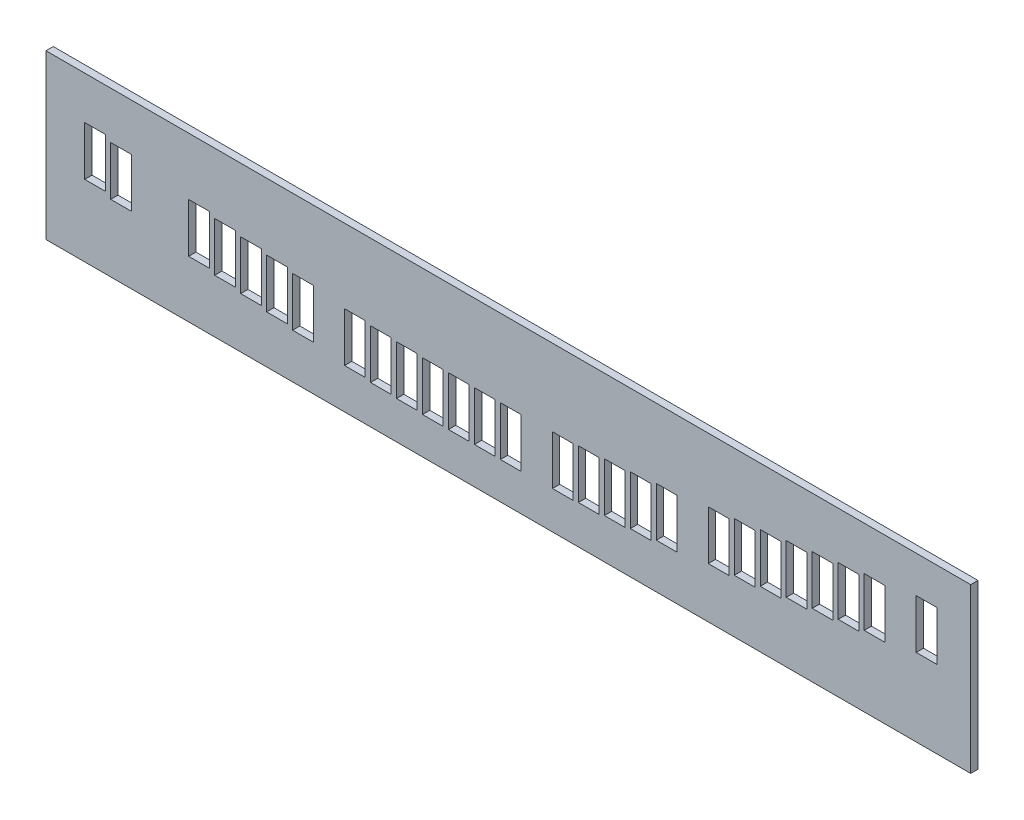
SolidWorks part; units mm, degrees
ref_plane "Front Plane" through (0, 0, 0) normal (0, 0, 1) x (1, 0, 0)
ref_plane "Top Plane" through (0, 0, 0) normal (0, 1, 0) x (1, 0, 0)
ref_plane "Right Plane" through (0, 0, 0) normal (1, 0, 0) x (0, 0, -1)
sketch "Sketch1" plane through (0, 0, 0) normal (0, 0, 1) x (1, 0, 0)
  line L0 (-0.0001, 1146.0049) -> (1685.9999, 1146.0049)
  line L1 (19.0499, 859.7049) -> (1666.8999, 859.7049)
  line L2 (-0.0001, 1146.0049) -> (-0.0001, 0)
  line L3 (19.0499, 1146.0049) -> (19.0499, 0)
  line L4 (104.9999, 1018.5049) -> (104.9999, 1092.5049)
  line L5 (104.9999, 1092.5049) -> (74.9999, 1092.5049)
  line L6 (74.9999, 1092.5049) -> (74.9999, 1018.5049)
  line L7 (74.9999, 1018.5049) -> (104.9999, 1018.5049)
  line L8 (1666.9499, 1146.0049) -> (1666.9499, 0)
  line L9 (1647.8999, 1146.0049) -> (1647.8999, 859.7049) construction
  line L10 (1685.9999, 1146.0049) -> (1685.9999, 0)
  line L11 (38.0999, 1146.0049) -> (38.0999, 859.7049) construction
  line L12 (143.9999, 992.5049) -> (173.9999, 992.5049)
  line L13 (173.9999, 992.5049) -> (173.9999, 918.5049)
  line L14 (173.9999, 918.5049) -> (143.9999, 918.5049)
  line L15 (143.9999, 918.5049) -> (143.9999, 992.5049)
  line L16 (189.9999, 992.5049) -> (219.9999, 992.5049)
  line L17 (219.9999, 992.5049) -> (219.9999, 918.5049)
  line L18 (219.9999, 918.5049) -> (189.9999, 918.5049)
  line L19 (189.9999, 918.5049) -> (189.9999, 992.5049)
  line L20 (235.9999, 992.5049) -> (265.9999, 992.5049)
  line L21 (265.9999, 992.5049) -> (265.9999, 918.5049)
  line L22 (265.9999, 918.5049) -> (235.9999, 918.5049)
  line L23 (235.9999, 918.5049) -> (235.9999, 992.5049)
  line L24 (196.9999, 1018.5049) -> (196.9999, 1092.5049)
  line L25 (196.9999, 1092.5049) -> (166.9999, 1092.5049)
  line L26 (166.9999, 1092.5049) -> (166.9999, 1018.5049)
  line L27 (166.9999, 1018.5049) -> (196.9999, 1018.5049)
  line L28 (242.9999, 1018.5049) -> (242.9999, 1092.5049)
  line L29 (242.9999, 1092.5049) -> (212.9999, 1092.5049)
  line L30 (212.9999, 1092.5049) -> (212.9999, 1018.5049)
  line L31 (212.9999, 1018.5049) -> (242.9999, 1018.5049)
  line L32 (281.9999, 992.5049) -> (311.9999, 992.5049)
  line L33 (311.9999, 992.5049) -> (311.9999, 918.5049)
  line L34 (311.9999, 918.5049) -> (281.9999, 918.5049)
  line L35 (281.9999, 918.5049) -> (281.9999, 992.5049)
  line L36 (327.9999, 992.5049) -> (357.9999, 992.5049)
  line L37 (357.9999, 992.5049) -> (357.9999, 918.5049)
  line L38 (357.9999, 918.5049) -> (327.9999, 918.5049)
  line L39 (327.9999, 918.5049) -> (327.9999, 992.5049)
  line L40 (373.9999, 992.5049) -> (403.9999, 992.5049)
  line L41 (403.9999, 992.5049) -> (403.9999, 918.5049)
  line L42 (403.9999, 918.5049) -> (373.9999, 918.5049)
  line L43 (373.9999, 918.5049) -> (373.9999, 992.5049)
  line L44 (419.9999, 992.5049) -> (449.9999, 992.5049)
  line L45 (449.9999, 992.5049) -> (449.9999, 918.5049)
  line L46 (449.9999, 918.5049) -> (419.9999, 918.5049)
  line L47 (419.9999, 918.5049) -> (419.9999, 992.5049)
  line L48 (334.9999, 1018.5049) -> (334.9999, 1092.5049)
  line L49 (334.9999, 1092.5049) -> (304.9999, 1092.5049)
  line L50 (304.9999, 1092.5049) -> (304.9999, 1018.5049)
  line L51 (304.9999, 1018.5049) -> (334.9999, 1018.5049)
  line L52 (380.9999, 1018.5049) -> (380.9999, 1092.5049)
  line L53 (380.9999, 1092.5049) -> (350.9999, 1092.5049)
  line L54 (350.9999, 1092.5049) -> (350.9999, 1018.5049)
  line L55 (350.9999, 1018.5049) -> (380.9999, 1018.5049)
  line L56 (426.9999, 1018.5049) -> (426.9999, 1092.5049)
  line L57 (426.9999, 1092.5049) -> (396.9999, 1092.5049)
  line L58 (396.9999, 1092.5049) -> (396.9999, 1018.5049)
  line L59 (396.9999, 1018.5049) -> (426.9999, 1018.5049)
  line L60 (465.9999, 992.5049) -> (495.9999, 992.5049)
  line L61 (495.9999, 992.5049) -> (495.9999, 918.5049)
  line L62 (495.9999, 918.5049) -> (465.9999, 918.5049)
  line L63 (465.9999, 918.5049) -> (465.9999, 992.5049)
  line L64 (511.9999, 992.5049) -> (541.9999, 992.5049)
  line L65 (541.9999, 992.5049) -> (541.9999, 918.5049)
  line L66 (541.9999, 918.5049) -> (511.9999, 918.5049)
  line L67 (511.9999, 918.5049) -> (511.9999, 992.5049)
  line L68 (557.9999, 992.5049) -> (587.9999, 992.5049)
  line L69 (587.9999, 992.5049) -> (587.9999, 918.5049)
  line L70 (587.9999, 918.5049) -> (557.9999, 918.5049)
  line L71 (557.9999, 918.5049) -> (557.9999, 992.5049)
  line L72 (518.9999, 1018.5049) -> (518.9999, 1092.5049)
  line L73 (518.9999, 1092.5049) -> (488.9999, 1092.5049)
  line L74 (488.9999, 1092.5049) -> (488.9999, 1018.5049)
  line L75 (488.9999, 1018.5049) -> (518.9999, 1018.5049)
  line L76 (564.9999, 1018.5049) -> (564.9999, 1092.5049)
  line L77 (564.9999, 1092.5049) -> (534.9999, 1092.5049)
  line L78 (534.9999, 1092.5049) -> (534.9999, 1018.5049)
  line L79 (534.9999, 1018.5049) -> (564.9999, 1018.5049)
  line L80 (603.9999, 992.5049) -> (633.9999, 992.5049)
  line L81 (633.9999, 992.5049) -> (633.9999, 918.5049)
  line L82 (633.9999, 918.5049) -> (603.9999, 918.5049)
  line L83 (603.9999, 918.5049) -> (603.9999, 992.5049)
  line L84 (649.9999, 992.5049) -> (679.9999, 992.5049)
  line L85 (679.9999, 992.5049) -> (679.9999, 918.5049)
  line L86 (679.9999, 918.5049) -> (649.9999, 918.5049)
  line L87 (649.9999, 918.5049) -> (649.9999, 992.5049)
  line L88 (695.9999, 992.5049) -> (725.9999, 992.5049)
  line L89 (725.9999, 992.5049) -> (725.9999, 918.5049)
  line L90 (725.9999, 918.5049) -> (695.9999, 918.5049)
  line L91 (695.9999, 918.5049) -> (695.9999, 992.5049)
  line L92 (741.9999, 992.5049) -> (771.9999, 992.5049)
  line L93 (771.9999, 992.5049) -> (771.9999, 918.5049)
  line L94 (771.9999, 918.5049) -> (741.9999, 918.5049)
  line L95 (741.9999, 918.5049) -> (741.9999, 992.5049)
  line L96 (656.9999, 1018.5049) -> (656.9999, 1092.5049)
  line L97 (656.9999, 1092.5049) -> (626.9999, 1092.5049)
  line L98 (626.9999, 1092.5049) -> (626.9999, 1018.5049)
  line L99 (626.9999, 1018.5049) -> (656.9999, 1018.5049)
  line L100 (702.9999, 1018.5049) -> (702.9999, 1092.5049)
  line L101 (702.9999, 1092.5049) -> (672.9999, 1092.5049)
  line L102 (672.9999, 1092.5049) -> (672.9999, 1018.5049)
  line L103 (672.9999, 1018.5049) -> (702.9999, 1018.5049)
  line L104 (748.9999, 1018.5049) -> (748.9999, 1092.5049)
  line L105 (748.9999, 1092.5049) -> (718.9999, 1092.5049)
  line L106 (718.9999, 1092.5049) -> (718.9999, 1018.5049)
  line L107 (718.9999, 1018.5049) -> (748.9999, 1018.5049)
  line L108 (787.9999, 992.5049) -> (817.9999, 992.5049)
  line L109 (817.9999, 992.5049) -> (817.9999, 918.5049)
  line L110 (817.9999, 918.5049) -> (787.9999, 918.5049)
  line L111 (787.9999, 918.5049) -> (787.9999, 992.5049)
  line L112 (833.9999, 992.5049) -> (863.9999, 992.5049)
  line L113 (863.9999, 992.5049) -> (863.9999, 918.5049)
  line L114 (863.9999, 918.5049) -> (833.9999, 918.5049)
  line L115 (833.9999, 918.5049) -> (833.9999, 992.5049)
  line L116 (879.9999, 992.5049) -> (909.9999, 992.5049)
  line L117 (909.9999, 992.5049) -> (909.9999, 918.5049)
  line L118 (909.9999, 918.5049) -> (879.9999, 918.5049)
  line L119 (879.9999, 918.5049) -> (879.9999, 992.5049)
  line L120 (840.9999, 1018.5049) -> (840.9999, 1092.5049)
  line L121 (840.9999, 1092.5049) -> (810.9999, 1092.5049)
  line L122 (810.9999, 1092.5049) -> (810.9999, 1018.5049)
  line L123 (810.9999, 1018.5049) -> (840.9999, 1018.5049)
  line L124 (886.9999, 1018.5049) -> (886.9999, 1092.5049)
  line L125 (886.9999, 1092.5049) -> (856.9999, 1092.5049)
  line L126 (856.9999, 1092.5049) -> (856.9999, 1018.5049)
  line L127 (856.9999, 1018.5049) -> (886.9999, 1018.5049)
  line L128 (925.9999, 992.5049) -> (955.9999, 992.5049)
  line L129 (955.9999, 992.5049) -> (955.9999, 918.5049)
  line L130 (955.9999, 918.5049) -> (925.9999, 918.5049)
  line L131 (925.9999, 918.5049) -> (925.9999, 992.5049)
  line L132 (971.9999, 992.5049) -> (1001.9999, 992.5049)
  line L133 (1001.9999, 992.5049) -> (1001.9999, 918.5049)
  line L134 (1001.9999, 918.5049) -> (971.9999, 918.5049)
  line L135 (971.9999, 918.5049) -> (971.9999, 992.5049)
  line L136 (1017.9999, 992.5049) -> (1047.9999, 992.5049)
  line L137 (1047.9999, 992.5049) -> (1047.9999, 918.5049)
  line L138 (1047.9999, 918.5049) -> (1017.9999, 918.5049)
  line L139 (1017.9999, 918.5049) -> (1017.9999, 992.5049)
  line L140 (1063.9999, 992.5049) -> (1093.9999, 992.5049)
  line L141 (1093.9999, 992.5049) -> (1093.9999, 918.5049)
  line L142 (1093.9999, 918.5049) -> (1063.9999, 918.5049)
  line L143 (1063.9999, 918.5049) -> (1063.9999, 992.5049)
  line L144 (978.9999, 1018.5049) -> (978.9999, 1092.5049)
  line L145 (978.9999, 1092.5049) -> (948.9999, 1092.5049)
  line L146 (948.9999, 1092.5049) -> (948.9999, 1018.5049)
  line L147 (948.9999, 1018.5049) -> (978.9999, 1018.5049)
  line L148 (1024.9999, 1018.5049) -> (1024.9999, 1092.5049)
  line L149 (1024.9999, 1092.5049) -> (994.9999, 1092.5049)
  line L150 (994.9999, 1092.5049) -> (994.9999, 1018.5049)
  line L151 (994.9999, 1018.5049) -> (1024.9999, 1018.5049)
  line L152 (1070.9999, 1018.5049) -> (1070.9999, 1092.5049)
  line L153 (1070.9999, 1092.5049) -> (1040.9999, 1092.5049)
  line L154 (1040.9999, 1092.5049) -> (1040.9999, 1018.5049)
  line L155 (1040.9999, 1018.5049) -> (1070.9999, 1018.5049)
  line L156 (1109.9999, 992.5049) -> (1139.9999, 992.5049)
  line L157 (1139.9999, 992.5049) -> (1139.9999, 918.5049)
  line L158 (1139.9999, 918.5049) -> (1109.9999, 918.5049)
  line L159 (1109.9999, 918.5049) -> (1109.9999, 992.5049)
  line L160 (1155.9999, 992.5049) -> (1185.9999, 992.5049)
  line L161 (1185.9999, 992.5049) -> (1185.9999, 918.5049)
  line L162 (1185.9999, 918.5049) -> (1155.9999, 918.5049)
  line L163 (1155.9999, 918.5049) -> (1155.9999, 992.5049)
  line L164 (1201.9999, 992.5049) -> (1231.9999, 992.5049)
  line L165 (1231.9999, 992.5049) -> (1231.9999, 918.5049)
  line L166 (1231.9999, 918.5049) -> (1201.9999, 918.5049)
  line L167 (1201.9999, 918.5049) -> (1201.9999, 992.5049)
  line L168 (1162.9999, 1018.5049) -> (1162.9999, 1092.5049)
  line L169 (1162.9999, 1092.5049) -> (1132.9999, 1092.5049)
  line L170 (1132.9999, 1092.5049) -> (1132.9999, 1018.5049)
  line L171 (1132.9999, 1018.5049) -> (1162.9999, 1018.5049)
  line L172 (1208.9999, 1018.5049) -> (1208.9999, 1092.5049)
  line L173 (1208.9999, 1092.5049) -> (1178.9999, 1092.5049)
  line L174 (1178.9999, 1092.5049) -> (1178.9999, 1018.5049)
  line L175 (1178.9999, 1018.5049) -> (1208.9999, 1018.5049)
  line L176 (1247.9999, 992.5049) -> (1277.9999, 992.5049)
  line L177 (1277.9999, 992.5049) -> (1277.9999, 918.5049)
  line L178 (1277.9999, 918.5049) -> (1247.9999, 918.5049)
  line L179 (1247.9999, 918.5049) -> (1247.9999, 992.5049)
  line L180 (1293.9999, 992.5049) -> (1323.9999, 992.5049)
  line L181 (1323.9999, 992.5049) -> (1323.9999, 918.5049)
  line L182 (1323.9999, 918.5049) -> (1293.9999, 918.5049)
  line L183 (1293.9999, 918.5049) -> (1293.9999, 992.5049)
  line L184 (1339.9999, 992.5049) -> (1369.9999, 992.5049)
  line L185 (1369.9999, 992.5049) -> (1369.9999, 918.5049)
  line L186 (1369.9999, 918.5049) -> (1339.9999, 918.5049)
  line L187 (1339.9999, 918.5049) -> (1339.9999, 992.5049)
  line L188 (1385.9999, 992.5049) -> (1415.9999, 992.5049)
  line L189 (1415.9999, 992.5049) -> (1415.9999, 918.5049)
  line L190 (1415.9999, 918.5049) -> (1385.9999, 918.5049)
  line L191 (1385.9999, 918.5049) -> (1385.9999, 992.5049)
  line L192 (1300.9999, 1018.5049) -> (1300.9999, 1092.5049)
  line L193 (1300.9999, 1092.5049) -> (1270.9999, 1092.5049)
  line L194 (1270.9999, 1092.5049) -> (1270.9999, 1018.5049)
  line L195 (1270.9999, 1018.5049) -> (1300.9999, 1018.5049)
  line L196 (1346.9999, 1018.5049) -> (1346.9999, 1092.5049)
  line L197 (1346.9999, 1092.5049) -> (1316.9999, 1092.5049)
  line L198 (1316.9999, 1092.5049) -> (1316.9999, 1018.5049)
  line L199 (1316.9999, 1018.5049) -> (1346.9999, 1018.5049)
  line L200 (1392.9999, 1018.5049) -> (1392.9999, 1092.5049)
  line L201 (1392.9999, 1092.5049) -> (1362.9999, 1092.5049)
  line L202 (1362.9999, 1092.5049) -> (1362.9999, 1018.5049)
  line L203 (1362.9999, 1018.5049) -> (1392.9999, 1018.5049)
  line L204 (1431.9999, 992.5049) -> (1461.9999, 992.5049)
  line L205 (1461.9999, 992.5049) -> (1461.9999, 918.5049)
  line L206 (1461.9999, 918.5049) -> (1431.9999, 918.5049)
  line L207 (1431.9999, 918.5049) -> (1431.9999, 992.5049)
  line L208 (19.1499, 330) -> (1666.9999, 330)
  line L209 (19.1499, 30) -> (1666.9999, 30)
  line L210 (38.0999, 330) -> (38.0999, 254.9027) construction
  line L211 (38.0999, 254.9027) -> (38.0999, 145.8996)
  line L212 (38.0999, 145.8996) -> (38.0999, 30) construction
  line L213 (1647.7999, 330) -> (1647.7999, 272.9027) construction
  line L214 (1647.7999, 272.9027) -> (1647.7999, 163.8996)
  line L215 (1647.7999, 163.8996) -> (1647.7999, 30) construction
  line L216 (783.9999, 97.8494) -> (783.9999, 183.5269)
  line L217 (783.9999, 183.5269) -> (819.9999, 183.5269)
  line L218 (819.9999, 183.5269) -> (819.9999, 97.8494)
  line L219 (819.9999, 97.8494) -> (783.9999, 97.8494)
  line L220 (738.7742, 97.8494) -> (738.7742, 183.5269)
  line L221 (738.7742, 183.5269) -> (774.7742, 183.5269)
  line L222 (774.7742, 183.5269) -> (774.7742, 97.8494)
  line L223 (774.7742, 97.8494) -> (738.7742, 97.8494)
  line L224 (693.5414, 97.8494) -> (693.5414, 183.5269)
  line L225 (693.5414, 183.5269) -> (729.5414, 183.5269)
  line L226 (729.5414, 183.5269) -> (729.5414, 97.8494)
  line L227 (729.5414, 97.8494) -> (693.5414, 97.8494)
  line L228 (648.31, 99.3494) -> (648.31, 185.0269)
  line L229 (648.31, 185.0269) -> (684.31, 185.0269)
  line L230 (684.31, 185.0269) -> (684.31, 99.3494)
  line L231 (684.31, 99.3494) -> (648.31, 99.3494)
  line L232 (603.0808, 100.8494) -> (603.0808, 186.5269)
  line L233 (603.0808, 186.5269) -> (639.0808, 186.5269)
  line L234 (639.0808, 186.5269) -> (639.0808, 100.8494)
  line L235 (639.0808, 100.8494) -> (603.0808, 100.8494)
  line L236 (557.849, 103.8494) -> (557.849, 189.5269)
  line L237 (557.849, 189.5269) -> (593.849, 189.5269)
  line L238 (593.849, 189.5269) -> (593.849, 103.8494)
  line L239 (593.849, 103.8494) -> (557.849, 103.8494)
  line L240 (467.3861, 111.8494) -> (467.3861, 197.5269)
  line L241 (467.3861, 197.5269) -> (503.3861, 197.5269)
  line L242 (503.3861, 197.5269) -> (503.3861, 111.8494)
  line L243 (503.3861, 111.8494) -> (467.3861, 111.8494)
  line L244 (422.1564, 116.8494) -> (422.1564, 202.5269)
  line L245 (422.1564, 202.5269) -> (458.1564, 202.5269)
  line L246 (458.1564, 202.5269) -> (458.1564, 116.8494)
  line L247 (458.1564, 116.8494) -> (422.1564, 116.8494)
  line L248 (376.927, 121.8494) -> (376.927, 207.5269)
  line L249 (376.927, 207.5269) -> (412.927, 207.5269)
  line L250 (412.927, 207.5269) -> (412.927, 121.8494)
  line L251 (412.927, 121.8494) -> (376.927, 121.8494)
  line L252 (331.6986, 126.8494) -> (331.6986, 212.5269)
  line L253 (331.6986, 212.5269) -> (367.6986, 212.5269)
  line L254 (367.6986, 212.5269) -> (367.6986, 126.8494)
  line L255 (367.6986, 126.8494) -> (331.6986, 126.8494)
  line L256 (286.4663, 132.8494) -> (286.4663, 218.5269)
  line L257 (286.4663, 218.5269) -> (322.4663, 218.5269)
  line L258 (322.4663, 218.5269) -> (322.4663, 132.8494)
  line L259 (322.4663, 132.8494) -> (286.4663, 132.8494)
  line L260 (150.7753, 150.8494) -> (150.7753, 236.5269)
  line L261 (150.7753, 236.5269) -> (186.7753, 236.5269)
  line L262 (186.7753, 236.5269) -> (186.7753, 150.8494)
  line L263 (186.7753, 150.8494) -> (150.7753, 150.8494)
  line L264 (829.2305, 97.8494) -> (829.2305, 183.5269)
  line L265 (829.2305, 183.5269) -> (865.2305, 183.5269)
  line L266 (865.2305, 183.5269) -> (865.2305, 97.8494)
  line L267 (865.2305, 97.8494) -> (829.2305, 97.8494)
  line L268 (919.6947, 99.3494) -> (919.6947, 185.0269)
  line L269 (919.6947, 185.0269) -> (955.6947, 185.0269)
  line L270 (955.6947, 185.0269) -> (955.6947, 99.3494)
  line L271 (955.6947, 99.3494) -> (919.6947, 99.3494)
  line L272 (964.9239, 100.8494) -> (964.9239, 186.5269)
  line L273 (964.9239, 186.5269) -> (1000.9239, 186.5269)
  line L274 (1000.9239, 186.5269) -> (1000.9239, 100.8494)
  line L275 (1000.9239, 100.8494) -> (964.9239, 100.8494)
  line L276 (1010.1557, 103.8494) -> (1010.1557, 189.5269)
  line L277 (1010.1557, 189.5269) -> (1046.1557, 189.5269)
  line L278 (1046.1557, 189.5269) -> (1046.1557, 103.8494)
  line L279 (1046.1557, 103.8494) -> (1010.1557, 103.8494)
  line L280 (1055.3838, 106.8494) -> (1055.3838, 192.5269)
  line L281 (1055.3838, 192.5269) -> (1091.3838, 192.5269)
  line L282 (1091.3838, 192.5269) -> (1091.3838, 106.8494)
  line L283 (1091.3838, 106.8494) -> (1055.3838, 106.8494)
  line L284 (1100.6186, 111.8494) -> (1100.6186, 197.5269)
  line L285 (1100.6186, 197.5269) -> (1136.6186, 197.5269)
  line L286 (1136.6186, 197.5269) -> (1136.6186, 111.8494)
  line L287 (1136.6186, 111.8494) -> (1100.6186, 111.8494)
  line L288 (1191.0777, 121.8494) -> (1191.0777, 207.5269)
  line L289 (1191.0777, 207.5269) -> (1227.0777, 207.5269)
  line L290 (1227.0777, 207.5269) -> (1227.0777, 121.8494)
  line L291 (1227.0777, 121.8494) -> (1191.0777, 121.8494)
  line L292 (1236.3061, 126.8494) -> (1236.3061, 212.5269)
  line L293 (1236.3061, 212.5269) -> (1272.3061, 212.5269)
  line L294 (1272.3061, 212.5269) -> (1272.3061, 126.8494)
  line L295 (1272.3061, 126.8494) -> (1236.3061, 126.8494)
  line L296 (1281.5384, 132.8494) -> (1281.5384, 218.5269)
  line L297 (1281.5384, 218.5269) -> (1317.5384, 218.5269)
  line L298 (1317.5384, 218.5269) -> (1317.5384, 132.8494)
  line L299 (1317.5384, 132.8494) -> (1281.5384, 132.8494)
  line L300 (1326.7683, 138.8494) -> (1326.7683, 224.5269)
  line L301 (1326.7683, 224.5269) -> (1362.7683, 224.5269)
  line L302 (1362.7683, 224.5269) -> (1362.7683, 138.8494)
  line L303 (1362.7683, 138.8494) -> (1326.7683, 138.8494)
  line L304 (1372.0007, 144.8494) -> (1372.0007, 230.5269)
  line L305 (1372.0007, 230.5269) -> (1408.0007, 230.5269)
  line L306 (1408.0007, 230.5269) -> (1408.0007, 144.8494)
  line L307 (1408.0007, 144.8494) -> (1372.0007, 144.8494)
  line L308 (1417.2294, 150.8494) -> (1417.2294, 236.5269)
  line L309 (1417.2294, 236.5269) -> (1453.2294, 236.5269)
  line L310 (1453.2294, 236.5269) -> (1453.2294, 150.8494)
  line L311 (1453.2294, 150.8494) -> (1417.2294, 150.8494)
  line L312 (1462.4592, 156.8494) -> (1462.4592, 242.5269)
  line L313 (1462.4592, 242.5269) -> (1498.4592, 242.5269)
  line L314 (1498.4592, 242.5269) -> (1498.4592, 156.8494)
  line L315 (1498.4592, 156.8494) -> (1462.4592, 156.8494)
  line L316 (1553.0199, 168.8494) -> (1553.0199, 254.5269)
  line L317 (1553.0199, 254.5269) -> (1589.0199, 254.5269)
  line L318 (1589.0199, 254.5269) -> (1589.0199, 168.8494)
  line L319 (1589.0199, 168.8494) -> (1553.0199, 168.8494)
sketch "Sketch2" plane through (0, 0, 0) normal (0, 0, 1) x (1, 0, 0)
  line L0 (1589.0199, 254.5269) -> (1589.0199, 168.8494) construction
  line L1 (1589.0199, 168.8494) -> (1553.0199, 168.8494) construction
  line L2 (1553.0199, 254.5269) -> (1589.0199, 254.5269) construction
  line L3 (1553.0199, 168.8494) -> (1553.0199, 254.5269) construction
  line L4 (1498.4592, 156.8494) -> (1462.4592, 156.8494) construction
  line L5 (1462.4592, 242.5269) -> (1498.4592, 242.5269) construction
  line L6 (1498.4592, 242.5269) -> (1498.4592, 156.8494) construction
  line L7 (1462.4592, 156.8494) -> (1462.4592, 242.5269) construction
  line L8 (1453.2294, 150.8494) -> (1417.2294, 150.8494) construction
  line L9 (1417.2294, 236.5269) -> (1453.2294, 236.5269) construction
  line L10 (1453.2294, 236.5269) -> (1453.2294, 150.8494) construction
  line L11 (1417.2294, 150.8494) -> (1417.2294, 236.5269) construction
  line L12 (1408.0007, 144.8494) -> (1372.0007, 144.8494) construction
  line L13 (1372.0007, 230.5269) -> (1408.0007, 230.5269) construction
  line L14 (1408.0007, 230.5269) -> (1408.0007, 144.8494) construction
  line L15 (1372.0007, 144.8494) -> (1372.0007, 230.5269) construction
  line L16 (1362.7683, 138.8494) -> (1326.7683, 138.8494) construction
  line L17 (1326.7683, 224.5269) -> (1362.7683, 224.5269) construction
  line L18 (1362.7683, 224.5269) -> (1362.7683, 138.8494) construction
  line L19 (1326.7683, 138.8494) -> (1326.7683, 224.5269) construction
  line L20 (1317.5384, 132.8494) -> (1281.5384, 132.8494) construction
  line L21 (1281.5384, 218.5269) -> (1317.5384, 218.5269) construction
  line L22 (1317.5384, 218.5269) -> (1317.5384, 132.8494) construction
  line L23 (1281.5384, 132.8494) -> (1281.5384, 218.5269) construction
  line L24 (1272.3061, 126.8494) -> (1236.3061, 126.8494) construction
  line L25 (1236.3061, 212.5269) -> (1272.3061, 212.5269) construction
  line L26 (1272.3061, 212.5269) -> (1272.3061, 126.8494) construction
  line L27 (1236.3061, 126.8494) -> (1236.3061, 212.5269) construction
  line L28 (1227.0777, 121.8494) -> (1191.0777, 121.8494) construction
  line L29 (1191.0777, 207.5269) -> (1227.0777, 207.5269) construction
  line L30 (1227.0777, 207.5269) -> (1227.0777, 121.8494) construction
  line L31 (1191.0777, 121.8494) -> (1191.0777, 207.5269) construction
  line L32 (1136.6186, 111.8494) -> (1100.6186, 111.8494) construction
  line L33 (1136.6186, 197.5269) -> (1136.6186, 111.8494) construction
  line L34 (1100.6186, 197.5269) -> (1136.6186, 197.5269) construction
  line L35 (1100.6186, 111.8494) -> (1100.6186, 197.5269) construction
  line L36 (1091.3838, 192.5269) -> (1091.3838, 106.8494) construction
  line L37 (1091.3838, 106.8494) -> (1055.3838, 106.8494) construction
  line L38 (1055.3838, 106.8494) -> (1055.3838, 192.5269) construction
  line L39 (1055.3838, 192.5269) -> (1091.3838, 192.5269) construction
  line L40 (1046.1557, 189.5269) -> (1046.1557, 103.8494) construction
  line L41 (1010.1557, 103.8494) -> (1010.1557, 189.5269) construction
  line L42 (1046.1557, 103.8494) -> (1010.1557, 103.8494) construction
  line L43 (1010.1557, 189.5269) -> (1046.1557, 189.5269) construction
  line L44 (1000.9239, 186.5269) -> (1000.9239, 100.8494) construction
  line L45 (955.6947, 185.0269) -> (955.6947, 99.3494) construction
  line L46 (964.9239, 100.8494) -> (964.9239, 186.5269) construction
  line L47 (964.9239, 186.5269) -> (1000.9239, 186.5269) construction
  line L48 (1000.9239, 100.8494) -> (964.9239, 100.8494) construction
  line L49 (955.6947, 99.3494) -> (919.6947, 99.3494) construction
  line L50 (919.6947, 185.0269) -> (955.6947, 185.0269) construction
  line L51 (919.6947, 99.3494) -> (919.6947, 185.0269) construction
  line L52 (865.2305, 97.8494) -> (829.2305, 97.8494) construction
  line L53 (829.2305, 183.5269) -> (865.2305, 183.5269) construction
  line L54 (783.9999, 183.5269) -> (819.9999, 183.5269) construction
  line L55 (819.9999, 97.8494) -> (783.9999, 97.8494) construction
  line L56 (774.7742, 97.8494) -> (738.7742, 97.8494) construction
  line L57 (738.7742, 183.5269) -> (774.7742, 183.5269) construction
  line L58 (693.5414, 183.5269) -> (729.5414, 183.5269) construction
  line L59 (729.5414, 97.8494) -> (693.5414, 97.8494) construction
  line L60 (684.31, 99.3494) -> (648.31, 99.3494) construction
  line L61 (648.31, 185.0269) -> (684.31, 185.0269) construction
  line L62 (639.0808, 100.8494) -> (603.0808, 100.8494) construction
  line L63 (593.849, 103.8494) -> (557.849, 103.8494) construction
  line L64 (603.0808, 186.5269) -> (639.0808, 186.5269) construction
  line L65 (557.849, 189.5269) -> (593.849, 189.5269) construction
  line L66 (865.2305, 183.5269) -> (865.2305, 97.8494) construction
  line L67 (829.2305, 97.8494) -> (829.2305, 183.5269) construction
  line L68 (819.9999, 183.5269) -> (819.9999, 97.8494) construction
  line L69 (783.9999, 97.8494) -> (783.9999, 183.5269) construction
  line L70 (774.7742, 183.5269) -> (774.7742, 97.8494) construction
  line L71 (738.7742, 97.8494) -> (738.7742, 183.5269) construction
  line L72 (729.5414, 183.5269) -> (729.5414, 97.8494) construction
  line L73 (693.5414, 97.8494) -> (693.5414, 183.5269) construction
  line L74 (684.31, 185.0269) -> (684.31, 99.3494) construction
  line L75 (648.31, 99.3494) -> (648.31, 185.0269) construction
  line L76 (639.0808, 186.5269) -> (639.0808, 100.8494) construction
  line L77 (603.0808, 100.8494) -> (603.0808, 186.5269) construction
  line L78 (593.849, 189.5269) -> (593.849, 103.8494) construction
  line L79 (557.849, 103.8494) -> (557.849, 189.5269) construction
  line L80 (503.3861, 197.5269) -> (503.3861, 111.8494) construction
  line L81 (322.4663, 218.5269) -> (322.4663, 132.8494) construction
  line L82 (467.3861, 111.8494) -> (467.3861, 197.5269) construction
  line L83 (467.3861, 197.5269) -> (503.3861, 197.5269) construction
  line L84 (503.3861, 111.8494) -> (467.3861, 111.8494) construction
  line L85 (458.1564, 116.8494) -> (422.1564, 116.8494) construction
  line L86 (422.1564, 202.5269) -> (458.1564, 202.5269) construction
  line L87 (458.1564, 202.5269) -> (458.1564, 116.8494) construction
  line L88 (422.1564, 116.8494) -> (422.1564, 202.5269) construction
  line L89 (412.927, 207.5269) -> (412.927, 121.8494) construction
  line L90 (376.927, 121.8494) -> (376.927, 207.5269) construction
  line L91 (412.927, 121.8494) -> (376.927, 121.8494) construction
  line L92 (376.927, 207.5269) -> (412.927, 207.5269) construction
  line L93 (367.6986, 126.8494) -> (331.6986, 126.8494) construction
  line L94 (367.6986, 212.5269) -> (367.6986, 126.8494) construction
  line L95 (331.6986, 126.8494) -> (331.6986, 212.5269) construction
  line L96 (331.6986, 212.5269) -> (367.6986, 212.5269) construction
  line L97 (322.4663, 132.8494) -> (286.4663, 132.8494) construction
  line L98 (286.4663, 218.5269) -> (322.4663, 218.5269) construction
  line L99 (286.4663, 132.8494) -> (286.4663, 218.5269) construction
  line L100 (186.7753, 150.8494) -> (150.7753, 150.8494) construction
  line L101 (150.7753, 236.5269) -> (186.7753, 236.5269) construction
  line L102 (186.7753, 236.5269) -> (186.7753, 150.8494) construction
  line L103 (150.7753, 150.8494) -> (150.7753, 236.5269) construction
  line L104 (1589.0199, 254.5269) -> (1589.0199, 168.8494)
  line L105 (1589.0199, 168.8494) -> (1553.0199, 168.8494)
  line L106 (1553.0199, 254.5269) -> (1589.0199, 254.5269)
  line L107 (1553.0199, 168.8494) -> (1553.0199, 254.5269)
  line L108 (1498.4592, 156.8494) -> (1462.4592, 156.8494)
  line L109 (1462.4592, 242.5269) -> (1498.4592, 242.5269)
  line L110 (1498.4592, 242.5269) -> (1498.4592, 156.8494)
  line L111 (1462.4592, 156.8494) -> (1462.4592, 242.5269)
  line L112 (1453.2294, 150.8494) -> (1417.2294, 150.8494)
  line L113 (1417.2294, 236.5269) -> (1453.2294, 236.5269)
  line L114 (1453.2294, 236.5269) -> (1453.2294, 150.8494)
  line L115 (1417.2294, 150.8494) -> (1417.2294, 236.5269)
  line L116 (1408.0007, 144.8494) -> (1372.0007, 144.8494)
  line L117 (1372.0007, 230.5269) -> (1408.0007, 230.5269)
  line L118 (1408.0007, 230.5269) -> (1408.0007, 144.8494)
  line L119 (1372.0007, 144.8494) -> (1372.0007, 230.5269)
  line L120 (1362.7683, 138.8494) -> (1326.7683, 138.8494)
  line L121 (1326.7683, 224.5269) -> (1362.7683, 224.5269)
  line L122 (1362.7683, 224.5269) -> (1362.7683, 138.8494)
  line L123 (1326.7683, 138.8494) -> (1326.7683, 224.5269)
  line L124 (1317.5384, 132.8494) -> (1281.5384, 132.8494)
  line L125 (1281.5384, 218.5269) -> (1317.5384, 218.5269)
  line L126 (1317.5384, 218.5269) -> (1317.5384, 132.8494)
  line L127 (1281.5384, 132.8494) -> (1281.5384, 218.5269)
  line L128 (1272.3061, 126.8494) -> (1236.3061, 126.8494)
  line L129 (1236.3061, 212.5269) -> (1272.3061, 212.5269)
  line L130 (1272.3061, 212.5269) -> (1272.3061, 126.8494)
  line L131 (1236.3061, 126.8494) -> (1236.3061, 212.5269)
  line L132 (1227.0777, 121.8494) -> (1191.0777, 121.8494)
  line L133 (1191.0777, 207.5269) -> (1227.0777, 207.5269)
  line L134 (1227.0777, 207.5269) -> (1227.0777, 121.8494)
  line L135 (1191.0777, 121.8494) -> (1191.0777, 207.5269)
  line L136 (1136.6186, 111.8494) -> (1100.6186, 111.8494)
  line L137 (1136.6186, 197.5269) -> (1136.6186, 111.8494)
  line L138 (1100.6186, 197.5269) -> (1136.6186, 197.5269)
  line L139 (1100.6186, 111.8494) -> (1100.6186, 197.5269)
  line L140 (1091.3838, 192.5269) -> (1091.3838, 106.8494)
  line L141 (1091.3838, 106.8494) -> (1055.3838, 106.8494)
  line L142 (1055.3838, 106.8494) -> (1055.3838, 192.5269)
  line L143 (1055.3838, 192.5269) -> (1091.3838, 192.5269)
  line L144 (1046.1557, 189.5269) -> (1046.1557, 103.8494)
  line L145 (1010.1557, 103.8494) -> (1010.1557, 189.5269)
  line L146 (1046.1557, 103.8494) -> (1010.1557, 103.8494)
  line L147 (1010.1557, 189.5269) -> (1046.1557, 189.5269)
  line L148 (1000.9239, 186.5269) -> (1000.9239, 100.8494)
  line L149 (955.6947, 185.0269) -> (955.6947, 99.3494)
  line L150 (964.9239, 100.8494) -> (964.9239, 186.5269)
  line L151 (964.9239, 186.5269) -> (1000.9239, 186.5269)
  line L152 (1000.9239, 100.8494) -> (964.9239, 100.8494)
  line L153 (955.6947, 99.3494) -> (919.6947, 99.3494)
  line L154 (919.6947, 185.0269) -> (955.6947, 185.0269)
  line L155 (919.6947, 99.3494) -> (919.6947, 185.0269)
  line L156 (865.2305, 97.8494) -> (829.2305, 97.8494)
  line L157 (829.2305, 183.5269) -> (865.2305, 183.5269)
  line L158 (783.9999, 183.5269) -> (819.9999, 183.5269)
  line L159 (819.9999, 97.8494) -> (783.9999, 97.8494)
  line L160 (774.7742, 97.8494) -> (738.7742, 97.8494)
  line L161 (738.7742, 183.5269) -> (774.7742, 183.5269)
  line L162 (693.5414, 183.5269) -> (729.5414, 183.5269)
  line L163 (729.5414, 97.8494) -> (693.5414, 97.8494)
  line L164 (684.31, 99.3494) -> (648.31, 99.3494)
  line L165 (648.31, 185.0269) -> (684.31, 185.0269)
  line L166 (639.0808, 100.8494) -> (603.0808, 100.8494)
  line L167 (593.849, 103.8494) -> (557.849, 103.8494)
  line L168 (603.0808, 186.5269) -> (639.0808, 186.5269)
  line L169 (557.849, 189.5269) -> (593.849, 189.5269)
  line L170 (865.2305, 183.5269) -> (865.2305, 97.8494)
  line L171 (829.2305, 97.8494) -> (829.2305, 183.5269)
  line L172 (819.9999, 183.5269) -> (819.9999, 97.8494)
  line L173 (783.9999, 97.8494) -> (783.9999, 183.5269)
  line L174 (774.7742, 183.5269) -> (774.7742, 97.8494)
  line L175 (738.7742, 97.8494) -> (738.7742, 183.5269)
  line L176 (729.5414, 183.5269) -> (729.5414, 97.8494)
  line L177 (693.5414, 97.8494) -> (693.5414, 183.5269)
  line L178 (684.31, 185.0269) -> (684.31, 99.3494)
  line L179 (648.31, 99.3494) -> (648.31, 185.0269)
  line L180 (639.0808, 186.5269) -> (639.0808, 100.8494)
  line L181 (603.0808, 100.8494) -> (603.0808, 186.5269)
  line L182 (593.849, 189.5269) -> (593.849, 103.8494)
  line L183 (557.849, 103.8494) -> (557.849, 189.5269)
  line L184 (503.3861, 197.5269) -> (503.3861, 111.8494)
  line L185 (322.4663, 218.5269) -> (322.4663, 132.8494)
  line L186 (467.3861, 111.8494) -> (467.3861, 197.5269)
  line L187 (467.3861, 197.5269) -> (503.3861, 197.5269)
  line L188 (503.3861, 111.8494) -> (467.3861, 111.8494)
  line L189 (458.1564, 116.8494) -> (422.1564, 116.8494)
  line L190 (422.1564, 202.5269) -> (458.1564, 202.5269)
  line L191 (458.1564, 202.5269) -> (458.1564, 116.8494)
  line L192 (422.1564, 116.8494) -> (422.1564, 202.5269)
  line L193 (412.927, 207.5269) -> (412.927, 121.8494)
  line L194 (376.927, 121.8494) -> (376.927, 207.5269)
  line L195 (412.927, 121.8494) -> (376.927, 121.8494)
  line L196 (376.927, 207.5269) -> (412.927, 207.5269)
  line L197 (367.6986, 126.8494) -> (331.6986, 126.8494)
  line L198 (367.6986, 212.5269) -> (367.6986, 126.8494)
  line L199 (331.6986, 126.8494) -> (331.6986, 212.5269)
  line L200 (331.6986, 212.5269) -> (367.6986, 212.5269)
  line L201 (322.4663, 132.8494) -> (286.4663, 132.8494)
  line L202 (286.4663, 218.5269) -> (322.4663, 218.5269)
  line L203 (286.4663, 132.8494) -> (286.4663, 218.5269)
  line L204 (186.7753, 150.8494) -> (150.7753, 150.8494)
  line L205 (150.7753, 236.5269) -> (186.7753, 236.5269)
  line L206 (186.7753, 236.5269) -> (186.7753, 150.8494)
  line L207 (150.7753, 150.8494) -> (150.7753, 236.5269)
  line L209 (19.0499, 1146.0049) -> (19.0499, 0) construction
  line L210 (19.0499, 318.5304) -> (1666.9499, 318.5304)
  line L211 (1666.9499, 1146.0049) -> (1666.9499, 0) construction
  line L213 (19.0499, 33.8487) -> (1666.9499, 33.8487)
  line L214 (1666.9499, 33.8487) -> (1666.9499, 318.5304)
  line L215 (19.0499, 318.5304) -> (19.0499, 33.8487)
extrude "Boss-Extrude1" add sketch "Sketch2" along normal blind 12.7
sketch "Sketch3" plane through (0, 0, 12.7) normal (0, 0, 1) x (1, 0, 0)
  line L0 (1666.9499, 318.5304) -> (19.0499, 318.5304) construction
  line L1 (1666.9499, 318.5304) -> (19.0499, 318.5304)
  line L2 (842.9999, 318.5304) -> (38.0999, 318.5304)
  line L3 (38.0999, 318.5304) -> (38.0999, 33.8487)
  line L4 (19.0499, 33.8487) -> (1666.9499, 33.8487) construction
  line L5 (38.0999, 33.8487) -> (19.0499, 33.8487)
  line L6 (19.0499, 318.5304) -> (19.0499, 33.8487) construction
  line L7 (19.0499, 33.8487) -> (19.0499, 318.5304)
  line L8 (19.0499, 318.5304) -> (38.0999, 318.5304)
  line L9 (842.9999, 318.5304) -> (1647.8999, 318.5304)
  line L10 (1647.8999, 318.5304) -> (1647.8999, 33.8487)
  line L11 (1647.8999, 33.8487) -> (1666.9499, 33.8487)
  line L12 (1666.9499, 33.8487) -> (1666.9499, 318.5304)
  line L13 (1647.8999, 318.5304) -> (1666.9499, 318.5304)
extrude "Cut-Extrude1" cut sketch "Sketch3" against normal through all contours L11 L12 L1 L10 | L7 L5 L3 L1
sketch "Sketch4" plane through (0, 0, 12.7) normal (0, 0, 1) x (1, 0, 0)
  line L0 (150.7753, 150.8494) -> (186.7753, 150.8494) construction
  line L1 (1553.0199, 168.8494) -> (1589.0199, 168.8494) construction
  line L2 (783.9999, 97.8494) -> (819.9999, 97.8494) construction
  line L3 (1647.8999, 318.5304) -> (1647.8999, 33.8487) construction
  line L4 (38.0999, 318.5304) -> (38.0999, 33.8487) construction
  line L5 (1647.8999, 318.5304) -> (1647.8999, 33.8487)
  line L6 (38.0999, 318.5304) -> (38.0999, 33.8487)
  line L7 (150.7753, 193.6881) -> (141.5453, 193.6881)
  line L8 (150.7753, 236.5269) -> (150.7753, 150.8494) construction
  line L9 (141.5453, 193.6881) -> (105.5453, 193.6881)
  line L10 (105.5453, 193.6881) -> (105.5453, 158.3386)
  line L11 (105.5453, 158.3386) -> (141.5453, 158.3386)
  line L12 (141.5453, 158.3386) -> (141.5453, 244.0186)
  line L13 (141.5453, 244.0186) -> (105.5453, 244.0186)
  line L14 (105.5453, 244.0186) -> (105.5453, 193.6881)
  arc A0 (38.0999, 170.4469) -> (1647.8999, 180.2216) centre (817.8348, 4319.7984) ccw
  point P0 (168.7753, 150.8494)
  point P1 (1571.0199, 168.8494)
  point P4 (801.9999, 97.8494)
extrude "Cut-Extrude2" cut sketch "Sketch4" against normal through all contours L13 L14 L9 L12 | L11 L12 L9 L10
sketch "Sketch5" plane through (0, 0, 12.7) normal (0, 0, 1) x (1, 0, 0)
  line L0 (865.2305, 183.5269) -> (919.6947, 185.0269)
  line L1 (892.4626, 184.2769) -> (892.4626, 33.8487)
  line L2 (38.0999, 33.8487) -> (1647.8999, 33.8487) construction
  line L3 (892.4626, 184.2769) -> (892.4626, 318.5304)
  line L4 (1647.8999, 318.5304) -> (38.0999, 318.5304) construction
ref_plane "Plane1" through (892.4626, 0, 0) normal (-1, 0, 0) x (0, 0, 1)
